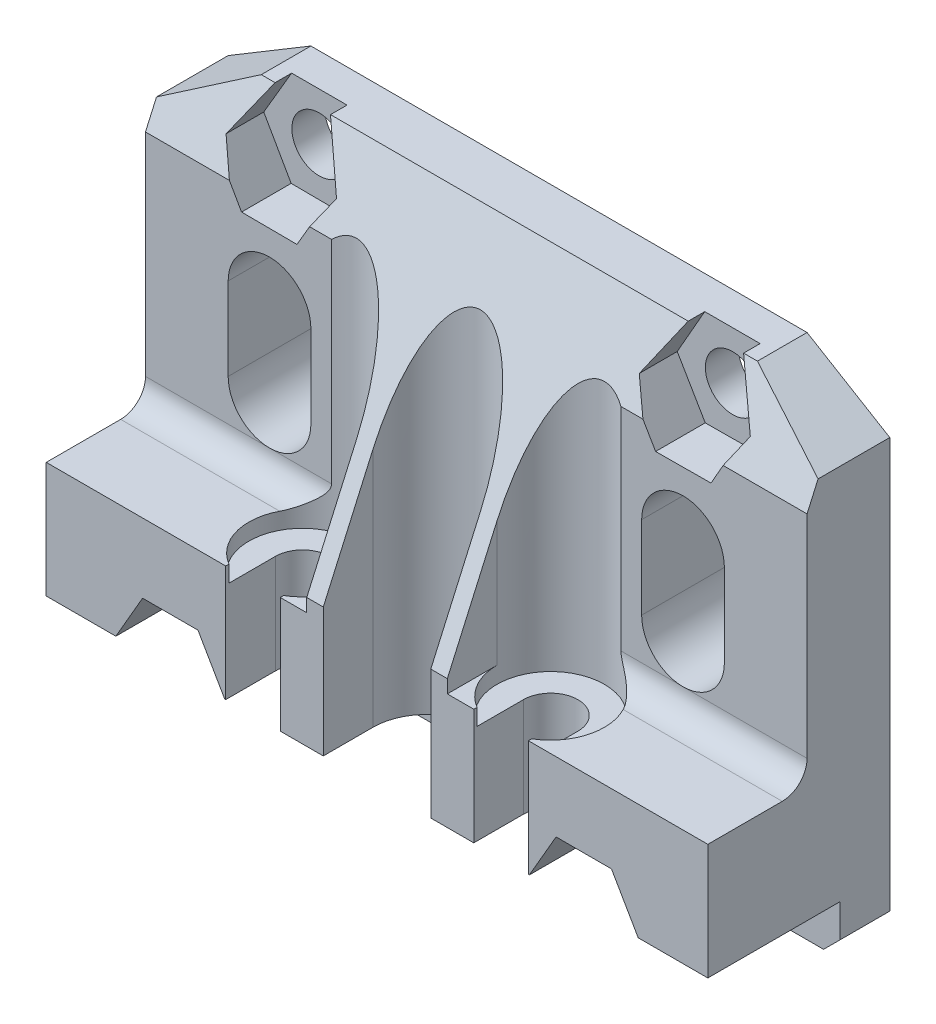
SolidWorks part; units mm, degrees
ref_plane "Front Plane" through (0, 0, 0) normal (0, 0, 1) x (1, 0, 0)
ref_plane "Top Plane" through (0, 0, 0) normal (0, 1, 0) x (1, 0, 0)
ref_plane "Right Plane" through (0, 0, 0) normal (1, 0, 0) x (0, 0, -1)
sketch "Sketch1" plane through (0, 0, 0) normal (0, 0, 1) x (1, 0, 0)
  line L1 (-20, 0) -> (20, 0)
  line L2 (-20, 0) -> (-20, 28.8)
  line L3 (-20, 28.8) -> (20, 28.8)
  line L4 (20, 0) -> (20, 28.8)
  dimension "D2" = 40
  dimension "D3" = 28.8
extrude "Boss-Extrude1" add sketch "Sketch1" along normal blind 11
chamfer "Chamfer2" distance 8 distance2 18 1 edges at (0, 28.8, 11)
sketch "Sketch10" plane through (0, 0, 11) normal (0, 0, 1) x (1, 0, 0)
  line L0 (-6.5, 28.8) -> (-6.5, 10)
  line L2 (-6.5, 10) -> (-20, 10)
  line L3 (-20, 10.8) -> (-20, 0) construction
  line L4 (0, 0) -> (0, 29.2248) construction
  line L5 (-6.5, 28.8) -> (-20, 28.8)
  line L6 (-20, 28.8) -> (-20, 10)
  line L7 (20, 28.8) -> (20, 10)
  line L8 (6.5, 28.8) -> (20, 28.8)
  line L9 (6.5, 10) -> (20, 10)
  line L10 (6.5, 28.8) -> (6.5, 10)
  line L11 (-20, 28.8) -> (20, 28.8) construction
  dimension "D1" = 10
  dimension "D2" = 6.5
extrude "Cut-Extrude7" cut sketch "Sketch10" against normal offset from surface (6 mm away) 5 up to face at (0, 14.4, 0)
fillet "Fillet1" radius 1.5 2 edges at (-13.25, 10, 5) (13.25, 10, 5)
sketch "Sketch11" plane through (0, 0, 11) normal (0, 0, 1) x (1, 0, 0)
  line L0 (20, 0) -> (20, 10) construction
  line L1 (-20, 0) -> (20, 0)
  line L2 (-20, 0) -> (-20, 3)
  line L3 (-20, 3) -> (20, 3)
  line L4 (20, 0) -> (20, 3)
  dimension "D1" = 3
extrude "Cut-Extrude8" cut sketch "Sketch11" against normal blind 8
chamfer "Chamfer3" [suppressed] distance 4 distance2 10
sketch "Sketch12" plane through (0, 28.8, 0) normal (0, 1, 0) x (1, 0, 0)
  line L0 (0, 0) -> (0, -14.4613) construction
  line L1 (-4.25, -8) -> (-4.25, -11)
  line L2 (-4.25, -11) -> (-10.75, -11)
  line L3 (-20, -11) -> (-6.5, -11) construction
  line L4 (-10.75, -11) -> (-10.75, -8)
  line L5 (6.5, -11) -> (-6.5, -11) construction
  arc A0 (-4.25, -8) -> (-10.75, -8) centre (-7.5, -8) ccw
  dimension "D1" = 3.25
  dimension "D2" = 8
  dimension "D3" = 7.5
extrude "Cut-Extrude9" cut sketch "Sketch12" against normal up to surface (18.8 mm away) up to face at (-13.25, 10, 8.75)
sketch "Sketch13" plane through (0, 10, 0) normal (0, 1, 0) x (1, 0, 0)
  line L0 (-9.15, -8) -> (-9.15, -11)
  line L1 (-20, -11) -> (-4.25, -11) construction
  line L2 (-9.15, -11) -> (-5.85, -11)
  line L3 (-5.85, -8) -> (-5.85, -11)
  arc A0 (-5.85, -8) -> (-9.15, -8) centre (-7.5, -8) ccw
  arc A1 (-4.25, -8) -> (-10.3831, -6.5) centre (-7.5, -8) ccw construction
  dimension "D1" = 3.3
extrude "Cut-Extrude10" cut sketch "Sketch13" against normal through all
sketch "Sketch3" plane through (0, 0, 0) normal (0, -1, 0) x (1, 0, 0)
  line L0 (0, 0) -> (0, 11) construction
  line L1 (-20, 11) -> (20, 11) construction
  line L2 (-3.25, 8) -> (-3.25, 11)
  line L3 (3.25, 8) -> (3.25, 11)
  line L4 (-3.25, 11) -> (3.25, 11)
  line L5 (-20, 0) -> (20, 0) construction
  arc A0 (-3.25, 8) -> (3.25, 8) centre (0, 8) ccw
  dimension "D1" = 8
  dimension "D2" = 6.5
extrude "Cut-Extrude2" cut sketch "Sketch3" against normal blind 30
sketch "Sketch4" plane through (0, 0, 11) normal (0, 0, 1) x (1, 0, 0)
  line L0 (0, 28.8) -> (0, 14.0803) construction
  line L1 (20, 28.8) -> (-20, 28.8) construction
  line L2 (-4, 20.8) -> (-4, 28.8)
  line L3 (4, 20.8) -> (4, 28.8)
  line L4 (-4, 28.8) -> (4, 28.8)
  arc A0 (-4, 20.8) -> (4, 20.8) centre (0, 20.8) ccw
  dimension "D2" = 4
  dimension "D1" = 8
extrude "Cut-Extrude3" [suppressed] cut sketch "Sketch4" against normal through all
sketch "Sketch2" plane through (0, 0, 11) normal (0, 0, 1) x (1, 0, 0)
  line L0 (0, 0) -> (0, 28.8) construction
  line L1 (20, 28.8) -> (-20, 28.8) construction
  line L2 (-12.5, 2.9) -> (12.5, 2.9) construction
  line L3 (-12.5, 25.9) -> (12.5, 25.9) construction
  line L4 (-12.5, 25.9) -> (-12.5, 2.9) construction
  circle A0 centre (-12.5, 2.9) radius 1.65
  circle A1 centre (12.5, 2.9) radius 1.65
  circle A2 centre (12.5, 25.9) radius 1.65
  circle A3 centre (-12.5, 25.9) radius 1.65
  dimension "D5" = 3.3
  dimension "D1" = 25
  dimension "D2" = 23
  dimension "D3" = 2.9
  dimension "D4" = 12.5
extrude "Cut-Extrude1" cut sketch "Sketch2" against normal through all
sketch "Sketch5" plane through (0, 0, 11) normal (0, 0, 1) x (1, 0, 0)
  line L0 (-13.8255, 29.3763) -> (-11.1423, 29.3763)
  line L1 (-9.1514, 25.8801) -> (-11.1423, 29.3763)
  line L2 (11.1423, 29.3763) -> (13.8255, 29.3763)
  line L3 (-13.8255, 29.3763) -> (-15.8486, 25.9199)
  line L4 (-15.8486, 25.9199) -> (-14.1916, 23.01)
  line L5 (-14.1916, 23.01) -> (-10.843, 22.9901)
  line L6 (-10.843, 22.9901) -> (-9.1514, 25.8801)
  line L19 (15.8486, 25.9199) -> (13.8255, 29.3763)
  line L21 (11.1423, 29.3763) -> (9.1514, 25.8801)
  line L22 (9.1514, 25.8801) -> (10.843, 22.9901)
  line L23 (10.843, 22.9901) -> (14.1916, 23.01)
  line L24 (14.1916, 23.01) -> (15.8486, 25.9199)
  line L26 (-10.81, 28.79) -> (-14.1585, 28.8099) [skipped]
  line L27 (14.1585, 28.8099) -> (10.81, 28.79) [skipped]
  circle A0 centre (-12.5, 25.9) radius 2.9 construction
  circle A3 centre (12.5, 25.9) radius 2.9 construction
  dimension "D1" = 5.8
extrude "Cut-Extrude4" cut sketch "Sketch5" against normal offset from surface (9 mm away) 2 up to face at (-10.85, 25.9, 0)
sketch "Sketch6" plane through (0, 3, 0) normal (0, -1, 0) x (1, 0, 0)
  line L0 (0, 0) -> (0, 11) construction
  line L2 (-2.75, 11) -> (2.75, 11)
  line L3 (0, 4.6514) -> (2.9, 6.3257)
  line L4 (2.9, 6.3257) -> (2.9, 9.6743)
  line L5 (-2.9, 9.6743) -> (-2.75, 9.7609)
  line L6 (2.9, 9.6743) -> (2.75, 9.7609)
  line L7 (-2.9, 9.6743) -> (-2.9, 6.3257)
  line L8 (-2.9, 6.3257) -> (0, 4.6514)
  line L9 (-2.75, 9.7609) -> (-2.75, 11)
  line L10 (0, 11.3486) -> (-2.9, 9.6743) [skipped]
  line L11 (2.9, 9.6743) -> (0, 11.3486) [skipped]
  line L12 (2.75, 9.7609) -> (2.75, 11)
  circle A0 centre (0, 8) radius 2.9 construction
  dimension "D2" = 5.8
  dimension "D3" = 5.5
  dimension "D1" = 8
extrude "Cut-Extrude5" [suppressed] cut sketch "Sketch6" against normal blind 5
sketch "Sketch7" [suppressed] plane through (0, 11, 0) normal (0, -1, 0) x (1, 0, 0)
  line L0 (0, 0) -> (0, 11) construction
  line L1 (2.9, 11) -> (-2.9, 11) construction
  line L2 (-1.5, 8.6874) -> (-1.5, 11)
  line L3 (-1.5, 11) -> (1.5, 11)
  line L4 (1.5, 11) -> (1.5, 8.6874)
  arc A0 (-1.5, 8.6874) -> (1.5, 8.6874) centre (0, 8) ccw
  dimension "D1" = 3.3
  dimension "D2" = 8
  dimension "D3" = 3
  dimension "D4" = 1.5
extrude "Cut-Extrude6" [suppressed] cut sketch "Sketch7" against normal through all
sketch "Sketch15" plane through (0, 10, 0) normal (0, 1, 0) x (1, 0, 0)
  circle A0 centre (-7.5, -8) radius 3.25
extrude "Cut-Extrude12" cut sketch "Sketch15" against normal blind 1
sketch "Sketch16" plane through (0, 0, 5) normal (0, 0, 1) x (1, 0, 0)
  line L0 (-12.5, 25.9) -> (-12.5, 2.9) construction
  line L1 (-15, 14) -> (-15, 19)
  line L2 (-10, 14) -> (-10, 19)
  arc A0 (-10, 19) -> (-15, 19) centre (-12.5, 19) ccw
  arc A1 (-15, 14) -> (-10, 14) centre (-12.5, 14) ccw
  dimension "D1" = 2.5
  dimension "D2" = 14
  dimension "D3" = 19
extrude "Cut-Extrude13" cut sketch "Sketch16" against normal through all
mirror "Mirror1" about plane through (0, 0, 0) normal (1, 0, 0) of "Cut-Extrude13", "Cut-Extrude10", "Cut-Extrude9", "Cut-Extrude12"
chamfer "Chamfer4" distance 3 distance2 5 1 edges at (20, 28.8, 1.5)
chamfer "Chamfer5" distance 5 distance2 3 1 edges at (-20, 28.8, 1.5)
chamfer "Chamfer6" [suppressed] distance 7 distance2 4
chamfer "Chamfer7" [suppressed] distance 4 distance2 7
sketch "Sketch14" plane through (0, 0, 11) normal (0, 0, 1) x (1, 0, 0)
  line L1 (-9.1514, 2.9) -> (-10.8257, 5.8)
  line L2 (-10.8257, 5.8) -> (-14.1743, 5.8)
  line L3 (-14.1743, 5.8) -> (-15.8486, 2.9)
  line L4 (-15.8486, 2.9) -> (-14.1743, 0)
  line L5 (-14.1743, 0) -> (-10.8257, 0)
  line L6 (-10.8257, 0) -> (-9.1514, 2.9)
  line L7 (15.8486, 2.9) -> (14.1743, 5.8)
  line L8 (14.1743, 5.8) -> (10.8257, 5.8)
  line L9 (10.8257, 5.8) -> (9.1514, 2.9)
  line L10 (9.1514, 2.9) -> (10.8257, 0)
  line L11 (10.8257, 0) -> (14.1743, 0)
  line L12 (14.1743, 0) -> (15.8486, 2.9)
  circle A0 centre (-12.5, 2.9) radius 2.9 construction
  circle A1 centre (12.5, 2.9) radius 2.9 construction
  arc A2 (-14.147, 3) -> (-10.853, 3) centre (-12.5, 2.9) ccw construction
  arc A3 (10.853, 3) -> (14.147, 3) centre (12.5, 2.9) ccw construction
  dimension "D1" = 5.8
extrude "Cut-Extrude11" cut sketch "Sketch14" against normal offset from surface (9.4 mm away) 1.6 up to face at (0, 18.2, 0)
chamfer "Chamfer8" distance 1 angle 45 2 edges at (-20, 0, 1.5) (20, 0, 1.5)
chamfer "Chamfer9" [suppressed] distance 0.5 angle 45
chamfer "Chamfer10" [suppressed] distance 4 angle 25
